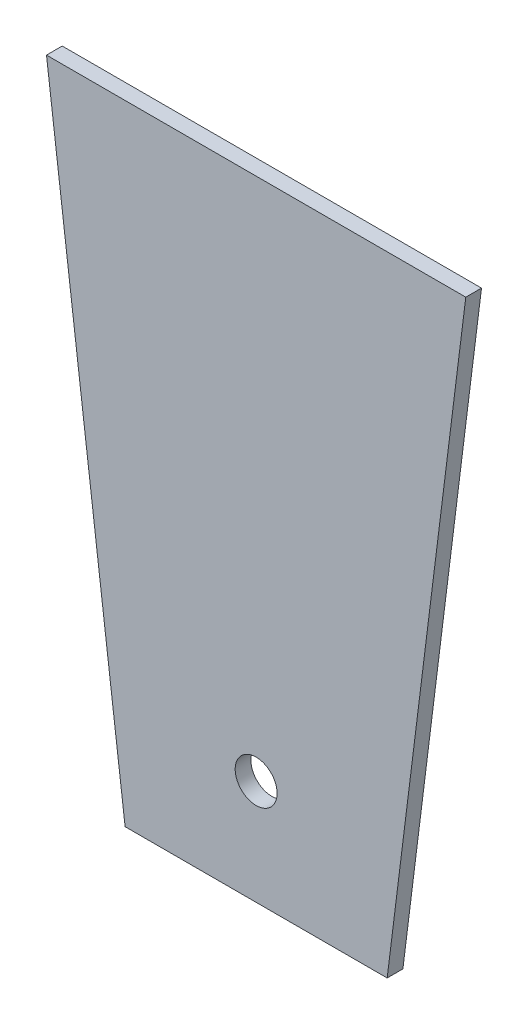
SolidWorks part; units mm, degrees
material "7075-O (SS)"
ref_plane "Front Plane" through (0, 0, 0) normal (0, 0, 1) x (1, 0, 0)
ref_plane "Top Plane" through (0, 0, 0) normal (0, 1, 0) x (1, 0, 0)
ref_plane "Right Plane" through (0, 0, 0) normal (1, 0, 0) x (0, 0, -1)
sketch "Sketch1" plane through (0, 0, 0) normal (0, 0, 1) x (1, 0, 0)
  line L0 (-40, 120) -> (40, 120)
  line L1 (-25, 0) -> (25, 0)
  line L2 (-40, 120) -> (-25, 0)
  line L3 (40, 120) -> (25, 0)
  circle A0 centre (0, 20) radius 4
  point P6 (0, 0)
  dimension "D5" = 8
  dimension "D6" = 20
  dimension "D7" = 40
  dimension "D1" = 80
  dimension "D2" = 120
  dimension "D3" = 40
  dimension "D4" = 50
extrude "Boss-Extrude1" add sketch "Sketch1" along normal blind 3
